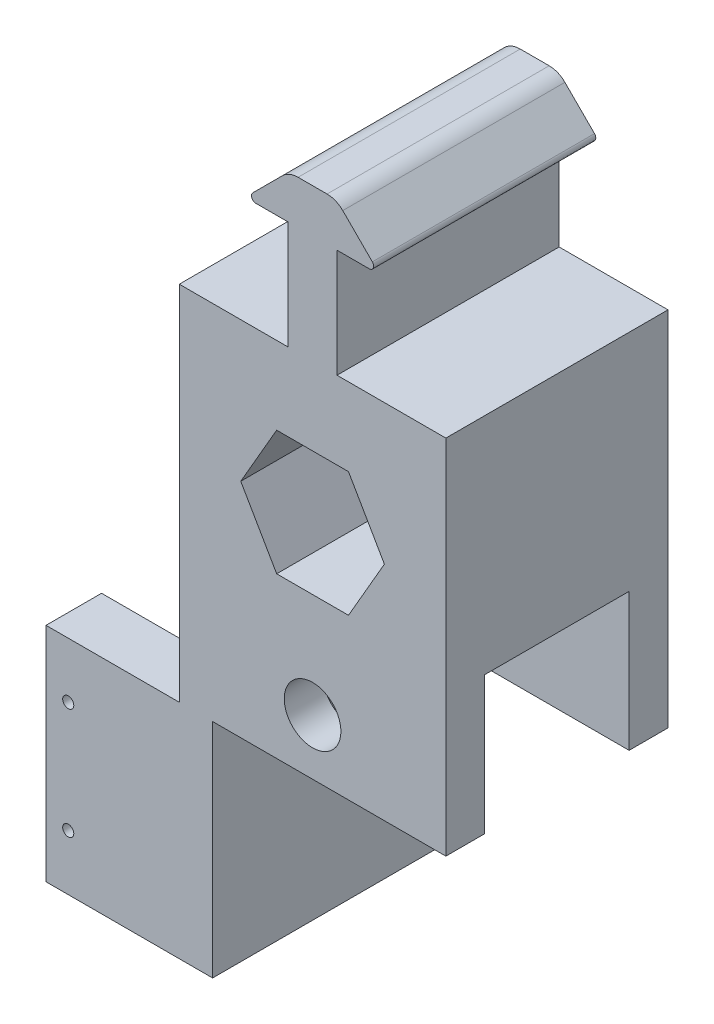
SolidWorks part; units mm, degrees
ref_plane "Front Plane" through (0, 0, 0) normal (0, 0, 1) x (1, 0, 0)
ref_plane "Top Plane" through (0, 0, 0) normal (0, 1, 0) x (1, 0, 0)
ref_plane "Right Plane" through (0, 0, 0) normal (1, 0, 0) x (0, 0, -1)
sketch "Sketch1" plane through (0, 0, 0) normal (0, 0, 1) x (1, 0, 0)
  line L0 (-15.24, 16.002) -> (-15.24, -25.4)
  line L1 (-4.1061, 7.112) -> (-8.2122, 0)
  line L2 (-8.2122, 0) -> (-4.1061, -7.112)
  line L3 (-4.1061, -7.112) -> (4.1061, -7.112)
  line L4 (4.1061, -7.112) -> (8.2122, 0)
  line L5 (8.2122, 0) -> (4.1061, 7.112)
  line L6 (4.1061, 7.112) -> (-4.1061, 7.112)
  line L7 (-15.24, -25.4) -> (15.24, -25.4)
  line L8 (15.24, -25.4) -> (15.24, 16.002)
  line L9 (-15.24, 16.002) -> (-2.794, 16.002)
  line L10 (-2.794, 16.002) -> (-2.794, 28.3845)
  line L11 (-2.794, 28.3845) -> (-6.477, 28.3845)
  line L12 (-6.8362, 29.2517) -> (-3.4525, 32.6355)
  line L13 (-1.6564, 33.3794) -> (1.6564, 33.3794)
  line L14 (0, 41.8096) -> (0, -25.778) construction
  line L15 (15.24, 16.002) -> (2.794, 16.002)
  line L16 (2.794, 16.002) -> (2.794, 28.3845)
  line L17 (6.8362, 29.2517) -> (3.4525, 32.6355)
  line L18 (2.794, 28.3845) -> (6.477, 28.3845)
  line L19 (-6.985, 28.8925) -> (6.985, 28.8925) construction
  circle A0 centre (0, 0) radius 7.112 construction
  arc A1 (-6.477, 28.3845) -> (-6.8362, 29.2517) centre (-6.477, 28.8925) cw
  arc A2 (-3.4525, 32.6355) -> (-1.6564, 33.3794) centre (-1.6564, 30.8394) cw
  arc A3 (3.4525, 32.6355) -> (1.6564, 33.3794) centre (1.6564, 30.8394) ccw
  arc A4 (6.477, 28.3845) -> (6.8362, 29.2517) centre (6.477, 28.8925) ccw
  point P18 (7.7034, 28.3845)
  point P21 (-4.6355, 28.3845)
  point P25 (-7.7034, 28.3845)
  point P29 (0, -25.4)
  point P35 (0, 33.3794)
  dimension "D7" = 0.508
  dimension "D8" = 2.54
  dimension "D1" = 14.224
  dimension "D2" = 21.2725
  dimension "D3" = 5.588
  dimension "D4" = 4.9949
  dimension "D5" = 135
  dimension "D6" = 13.97
  dimension "D9" = 25.4
  dimension "D10" = 8.89
  dimension "D11" = 15.24
extrude "Boss-Extrude1" add sketch "Sketch1" along normal mid plane 25.4
sketch "Sketch10" plane through (0, 0, 0) normal (0, 0, 1) x (1, 0, 0)
  line L0 (-15.24, -25.4) -> (-15.24, -46.99)
  line L1 (-15.24, -46.99) -> (-30.48, -46.99)
  line L2 (-30.48, -46.99) -> (-30.48, -50.8)
  line L3 (-30.48, -50.8) -> (-11.43, -50.8)
  line L4 (-11.43, -50.8) -> (-11.43, -25.4)
  line L5 (-15.24, -25.4) -> (15.24, -25.4) construction
  line L6 (-15.24, -25.4) -> (-11.43, -25.4)
  dimension "D1" = 19.05
  dimension "D2" = 21.59
  dimension "D3" = 3.81
extrude "Boss-Extrude4" add sketch "Sketch10" along normal up to surface and the other way up to surface up to face at (0, 19.8373, 12.7) other way up to face at (0, 19.8373, -12.7)
sketch "Sketch6" plane through (15.24, 0, 0) normal (1, 0, 0) x (0, 0, -1)
  line L0 (-12.7, -7.112) -> (12.7, -7.112) construction
  line L1 (-12.7, -7.112) -> (12.7, -7.112) construction
  line L2 (-8.255, -25.4) -> (-8.255, -9.652)
  line L3 (-8.255, -9.652) -> (8.255, -9.652)
  line L11 (-8.255, -25.4) -> (8.255, -25.4)
  line L12 (8.255, -9.652) -> (8.255, -25.4)
  point P10 (0, -9.652)
  dimension "D2" = 16.51
  dimension "D3" = 2.54
  dimension "D1" = 15.748
extrude "Cut-Extrude2" cut sketch "Sketch6" against normal through all
sketch "Sketch11" plane through (0, -46.99, 0) normal (0, 1, 0) x (1, 0, 0)
  line L0 (-30.48, -12.7) -> (-30.48, 12.7) construction
  line L1 (-15.24, -12.7) -> (-15.24, 12.7) construction
  line L2 (-30.48, -3.81) -> (-30.48, 3.81)
  line L3 (-15.24, -3.81) -> (-15.24, 3.81)
  line L4 (-30.48, 3.81) -> (-15.24, 3.81)
  line L5 (-30.48, -3.81) -> (-15.24, -3.81)
  point P8 (-15.24, 0)
  point P9 (-30.48, 0)
  dimension "D1" = 7.62
extrude "Cut-Extrude3" cut sketch "Sketch11" against normal up to surface (3.81 mm away) up to face at (-20.955, -50.8, 0)
sketch "Sketch15" plane through (0, 0, 12.7) normal (0, 0, 1) x (1, 0, 0)
  line L1 (-4.1061, -7.112) -> (4.1061, -7.112) construction
  circle A0 centre (0, -19.05) radius 3.2385
  point P7 (0, -7.112)
  dimension "D1" = 6.477
  dimension "D2" = 11.938
extrude "Cut-Extrude4" cut sketch "Sketch15" against normal up to surface (25.4 mm away) up to face at (-4.191, 6.0908, -12.7)
sketch "Sketch16" plane through (-15.24, 0, 0) normal (-1, 0, 0) x (0, 0, 1)
  line L0 (12.7, -46.99) -> (3.81, -46.99) construction
  line L1 (-3.81, -46.99) -> (-12.7, -46.99) construction
  line L2 (12.7, -46.99) -> (6.35, -46.99)
  line L3 (-6.35, -46.99) -> (-12.7, -46.99)
  line L4 (-12.7, -46.99) -> (-12.7, -25.4)
  line L5 (-12.7, 16.002) -> (-12.7, -46.99) construction
  line L6 (-12.7, -25.4) -> (-6.35, -25.4)
  line L7 (-6.35, -25.4) -> (-6.35, -46.99)
  line L8 (6.35, -46.99) -> (6.35, -25.4)
  line L9 (6.35, -25.4) -> (12.7, -25.4)
  line L10 (12.7, 16.002) -> (12.7, -46.99) construction
  line L11 (12.7, -25.4) -> (12.7, -46.99)
  line L12 (8.255, -25.4) -> (-8.255, -25.4) construction
  dimension "D1" = 6.35
extrude "Boss-Extrude5" add sketch "Sketch16" along normal blind 15.24
sketch "Sketch17" plane through (0, 0, 12.7) normal (0, 0, 1) x (1, 0, 0)
  line L0 (-30.48, -25.4) -> (-15.24, -25.4) construction
  circle A0 centre (-27.94, -31.75) radius 0.635
  circle A1 centre (-27.94, -44.45) radius 0.635
  dimension "D3" = 1.27
  dimension "D1" = 12.7
  dimension "D2" = 12.7
  dimension "D4" = 6.35
extrude "Cut-Extrude5" cut sketch "Sketch17" against normal through all
